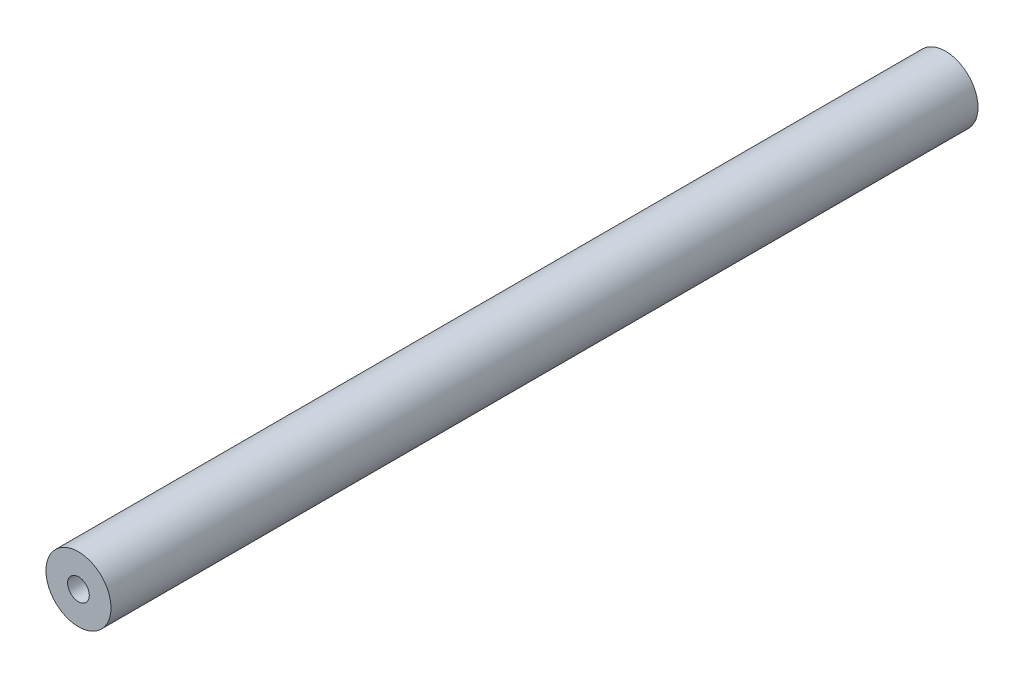
SolidWorks part; units mm, degrees
ref_plane "Alzado" through (0, 0, 0) normal (0, 0, 1) x (1, 0, 0)
ref_plane "Planta" through (0, 0, 0) normal (0, 1, 0) x (1, 0, 0)
ref_plane "Vista lateral" through (0, 0, 0) normal (1, 0, 0) x (0, 0, -1)
sketch "Croquis1" plane through (0, 0, 0) normal (0, 0, 1) x (1, 0, 0)
  circle A0 centre (0, 0) radius 12.5
  circle A1 centre (0, 0) radius 37.5
  dimension "D1" = 25
  dimension "D2" = 75
extrude "Saliente-Extruir1" add sketch "Croquis1" along normal blind 1000
